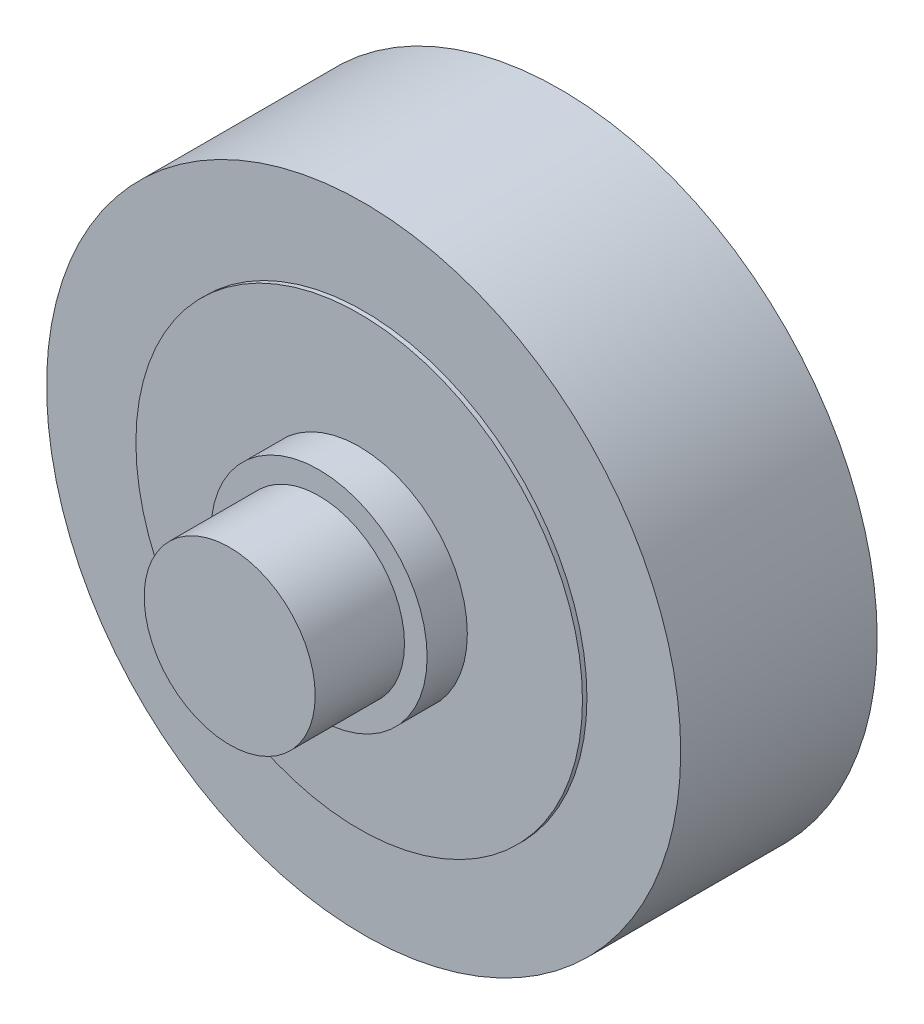
SolidWorks part; units mm, degrees
ref_plane "Front Plane" through (0, 0, 0) normal (0, 0, 1) x (1, 0, 0)
ref_plane "Top Plane" through (0, 0, 0) normal (0, 1, 0) x (1, 0, 0)
ref_plane "Right Plane" through (0, 0, 0) normal (1, 0, 0) x (0, 0, -1)
sketch "Sketch1" plane through (0, 0, 0) normal (0, 0, 1) x (1, 0, 0)
  circle A0 centre (0, 0) radius 71
  circle A1 centre (0, 0) radius 50
  dimension "D1" = 142
  dimension "D2" = 100
extrude "Boss-Extrude1" add sketch "Sketch1" along normal blind 44
sketch "Sketch2" plane through (0, 0, 0) normal (0, 0, 1) x (1, 0, 0)
  circle A0 centre (0, 0) radius 24.2163
  circle A1 centre (0, 0) radius 19.1503
extrude "Boss-Extrude2" add sketch "Sketch2" along normal blind 54 and the other way blind 10 separate body
sketch "Sketch3" plane through (0, 0, 0) normal (0, 0, 1) x (1, 0, 0)
  circle A0 centre (0, 0) radius 19.1503
extrude "Boss-Extrude3" add sketch "Sketch3" against normal blind 30 separate body
sketch "Sketch4" plane through (0, 0, 0) normal (0, 0, 1) x (1, 0, 0)
  circle A0 centre (0, 0) radius 19.1503
extrude "Boss-Extrude4" add sketch "Sketch4" along normal blind 74 separate body
sketch "Sketch7" plane through (0, 0, 44) normal (0, 0, 1) x (1, 0, 0)
  circle A0 centre (0, 0) radius 50
  circle A1 centre (0, 0) radius 24.2163
extrude "Boss-Extrude5" add sketch "Sketch7" along normal blind 1 and the other way blind 44
